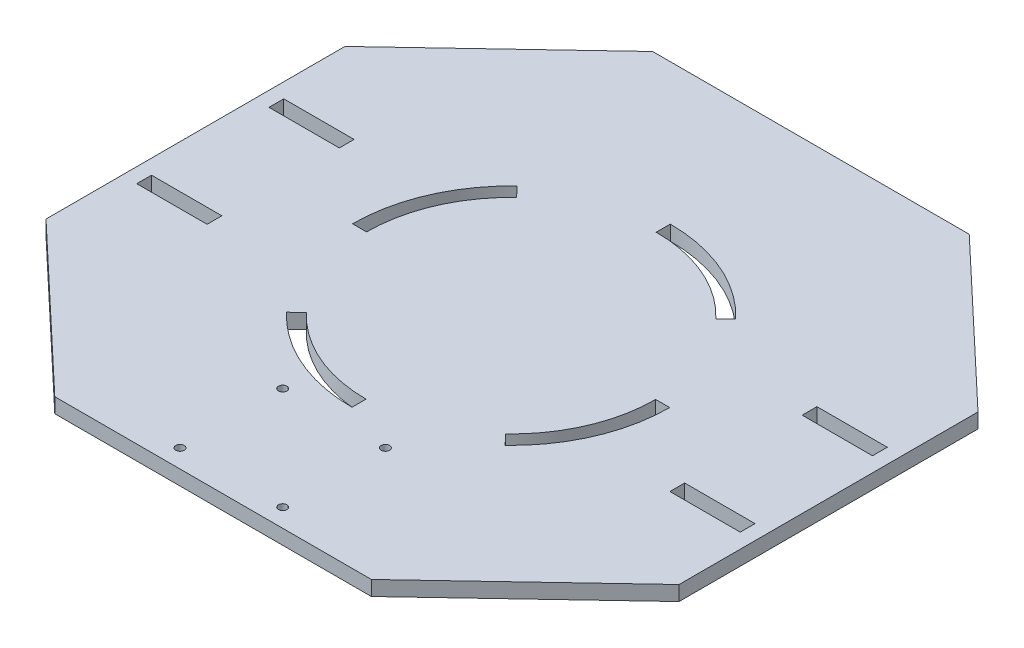
SolidWorks part; units mm, degrees
ref_plane "Front Plane" through (0, 0, 0) normal (0, 0, 1) x (1, 0, 0)
ref_plane "Top Plane" through (0, 0, 0) normal (0, 1, 0) x (1, 0, 0)
ref_plane "Right Plane" through (0, 0, 0) normal (1, 0, 0) x (0, 0, -1)
sketch "Sketch1" plane through (0, 0, 0) normal (0, 1, 0) x (1, 0, 0)
  line L1 (0, 0) -> (228.6, 0)
  line L2 (0, 0) -> (0, 215.9)
  line L3 (0, 215.9) -> (228.6, 215.9)
  line L4 (228.6, 0) -> (228.6, 215.9)
  dimension "D1" = 228.6
  dimension "D2" = 215.9
extrude "Boss-Extrude1" add sketch "Sketch1" along normal blind 5.334 contours L3 L4 L1 L2
sketch "Sketch14" plane through (0, 5.334, 0) normal (0, 1, 0) x (1, 0, 0)
  line L1 (0, 215.9) -> (228.6, 215.9) construction
  line L2 (0, 0) -> (228.6, 0) construction
  line L3 (0, 161.925) -> (228.6, 161.925) construction
  line L4 (0, 0) -> (0, 215.9) construction
  line L5 (228.6, 0) -> (228.6, 215.9) construction
  line L6 (0, 53.975) -> (228.6, 53.975) construction
  line L7 (57.15, 215.9) -> (57.15, 0) construction
  line L8 (171.45, 215.9) -> (171.45, 0) construction
sketch "Sketch13" plane through (0, 5.334, 0) normal (0, 1, 0) x (1, 0, 0)
  line L0 (0, 107.95) -> (228.6, 107.95) construction
  line L1 (0, 0) -> (0, 215.9) construction
  line L2 (228.6, 0) -> (228.6, 215.9) construction
  line L3 (0, 215.9) -> (0, 161.925)
  line L4 (0, 161.925) -> (57.15, 215.9)
  line L5 (57.15, 215.9) -> (0, 215.9)
  line L6 (114.3, 215.9) -> (114.3, 0) construction
  line L7 (0, 215.9) -> (228.6, 215.9) construction
  line L8 (0, 0) -> (228.6, 0) construction
  line L9 (228.6, 161.925) -> (171.45, 215.9)
  line L10 (228.6, 215.9) -> (228.6, 161.925)
  line L11 (171.45, 215.9) -> (228.6, 215.9)
  line L12 (228.6, 0) -> (228.6, 53.975)
  line L13 (171.45, 0) -> (228.6, 0)
  line L14 (228.6, 53.975) -> (171.45, 0)
  line L15 (0, 53.975) -> (57.15, 0)
  line L16 (0, 0) -> (0, 53.975)
  line L17 (57.15, 0) -> (0, 0)
sketch "Sketch6" plane through (0, 5.334, 0) normal (0, 1, 0) x (1, 0, 0)
  line L0 (114.3, 215.9) -> (114.3, 0) construction
  line L1 (0, 215.9) -> (228.6, 215.9) construction
  line L2 (0, 0) -> (228.6, 0) construction
  line L3 (0, 107.95) -> (228.6, 107.95) construction
  line L4 (0, 0) -> (0, 215.9) construction
  line L5 (228.6, 0) -> (228.6, 215.9) construction
  line L6 (228.6, 215.9) -> (0, 0) construction
  line L7 (0, 215.9) -> (228.6, 0) construction
  line L8 (114.3, 165.1) -> (114.3, 160.02)
  line L9 (155.8488, 147.1905) -> (152.1556, 143.7025)
  circle A0 centre (114.3, 107.95) radius 52.07
  arc A1 (114.3, 165.1) -> (155.8488, 147.1905) centre (114.3, 107.95) cw
  arc A2 (114.3, 160.02) -> (152.1556, 143.7025) centre (114.3, 107.95) cw
  dimension "D1" = 5.08
extrude "Cut-Extrude1" cut sketch "Sketch6" against normal through all contours A1 L8 A0 L9
pattern_circular "CirPattern1" count 4 over 360 about axis through (114.2033, 0, -107.7256) along (0, 1, 0) of "Cut-Extrude1"
sketch "Sketch8" plane through (0, 5.334, 0) normal (0, 1, 0) x (1, 0, 0)
  line L0 (0, 107.95) -> (228.6, 107.95) construction
  line L1 (5.334, 134.493) -> (30.734, 134.493)
  line L2 (5.334, 134.493) -> (5.334, 129.159)
  line L3 (5.334, 129.159) -> (30.734, 129.159)
  line L4 (30.734, 134.493) -> (30.734, 129.159)
  line L5 (0, 0) -> (0, 215.9) construction
  line L6 (228.6, 0) -> (228.6, 215.9) construction
  line L11 (114.3, 215.9) -> (114.3, 0) construction
  line L12 (0, 215.9) -> (228.6, 215.9) construction
  line L13 (0, 0) -> (228.6, 0) construction
  line L18 (223.266, 129.159) -> (197.866, 129.159)
  line L19 (197.866, 134.493) -> (197.866, 129.159)
  line L20 (223.266, 134.493) -> (197.866, 134.493)
  line L21 (223.266, 134.493) -> (223.266, 129.159)
  line L22 (223.266, 81.407) -> (223.266, 86.741)
  line L23 (223.266, 81.407) -> (197.866, 81.407)
  line L24 (197.866, 81.407) -> (197.866, 86.741)
  line L25 (223.266, 86.741) -> (197.866, 86.741)
  line L26 (5.334, 86.741) -> (30.734, 86.741)
  line L27 (30.734, 81.407) -> (30.734, 86.741)
  line L28 (5.334, 81.407) -> (30.734, 81.407)
  line L29 (5.334, 81.407) -> (5.334, 86.741)
  dimension "MotorMount1" = 25.4
  dimension "D2" = 5.334
  dimension "D1" = 21.209
  dimension "D5" = 5.334
extrude "Cut-Extrude2" cut sketch "Sketch8" against normal through all contours L2 L1 L4 L3 | L25 L24 L23 L22 | L18 L19 L20 L21 | L26 L27 L28 L29
sketch "Sketch11" plane through (0, 5.334, 0) normal (0, 1, 0) x (1, 0, 0)
  line L0 (114.3, 215.9) -> (114.3, 0) construction
  line L1 (0, 215.9) -> (228.6, 215.9) construction
  line L2 (0, 0) -> (228.6, 0) construction
  line L3 (92.71, 25.146) -> (135.89, 25.146) construction
  circle A0 centre (95.758, 6.604) radius 1.524
  circle A1 centre (132.842, 6.604) radius 1.524
  circle A2 centre (132.842, 43.688) radius 1.524
  circle A3 centre (95.758, 43.688) radius 1.524
extrude "Cut-Extrude4" cut sketch "Sketch11" against normal through all
extrude "Cut-Extrude5" cut sketch "Sketch13" against normal through all
equation "\"GMaterial\" = \"MDF\""
equation "\"MDF\"= 0.21in"
equation "\"Foamcore\"= 0.2in"
equation "\"D1@Boss-Extrude1\"=\"GMaterial\""
equation "\"D2@Sketch8\"=\"GMaterial\""
equation "\"D1@Sketch8\"=1.67/2"
equation "\"D5@Sketch8\"=\"GMaterial\""
equation "\"D1@Sketch6\"=\"Foamcore\""
